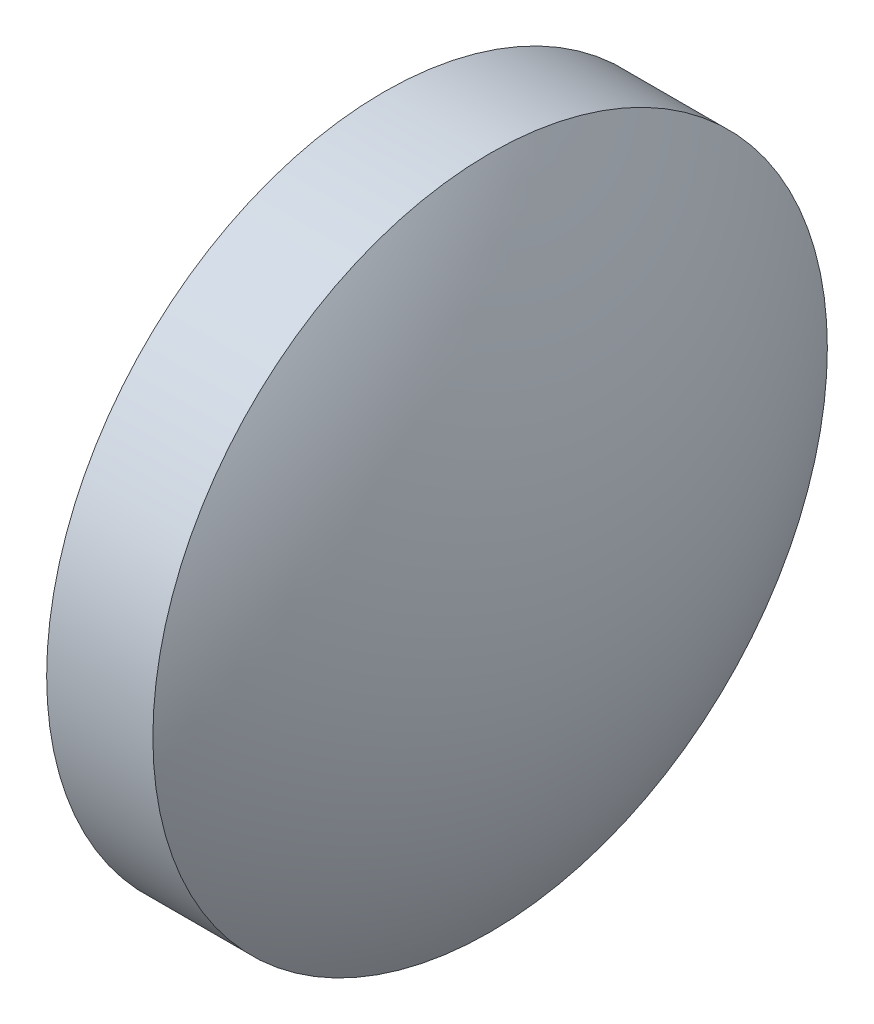
SolidWorks part; units mm, degrees
ref_plane "前视基准面" through (0, 0, 0) normal (0, 0, 1) x (1, 0, 0)
ref_plane "上视基准面" through (0, 0, 0) normal (0, 1, 0) x (1, 0, 0)
ref_plane "右视基准面" through (0, 0, 0) normal (1, 0, 0) x (0, 0, -1)
sketch "草图1" plane through (0, 0, 0) normal (0, 0, 1) x (1, 0, 0)
  line L0 (39.6527, 24.3081) -> (46.7386, 24.3081) construction
  line L1 (42.2291, 30.6581) -> (44.2291, 30.6581)
  line L2 (44.2291, 30.6581) -> (44.2291, 17.9581)
  line L3 (44.2291, 17.9581) -> (42.2291, 17.9581)
  line L4 (42.2291, 17.9581) -> (42.2291, 30.6581)
  arc A0 (42.2291, 30.6581) -> (42.2291, 17.9581) centre (52.5301, 24.3081) ccw
  arc A1 (44.2291, 17.9581) -> (44.2291, 30.6581) centre (33.9281, 24.3081) ccw
  dimension "D1" = 12.7
  dimension "D2" = 2.0001
revolve "旋转1" add sketch "草图1" angle 360 about L0
